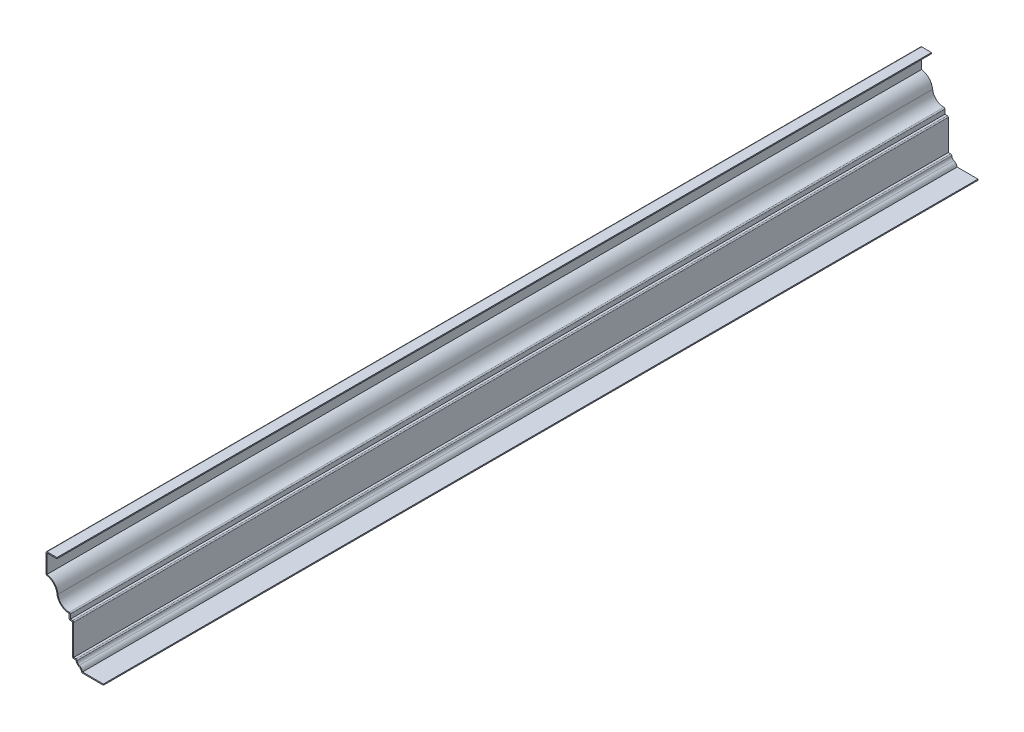
SolidWorks part; units mm, degrees
ref_plane "Front Plane" through (0, 0, 0) normal (0, 0, 1) x (1, 0, 0)
ref_plane "Top Plane" through (0, 0, 0) normal (0, 1, 0) x (1, 0, 0)
ref_plane "Right Plane" through (0, 0, 0) normal (1, 0, 0) x (0, 0, -1)
sketch "Sketch1" plane through (0, 0, 0) normal (0, 0, 1) x (1, 0, 0)
  line L0 (0, 0) -> (-25.4, 0)
  line L1 (-31.75, 9.525) -> (-35.7188, 9.525)
  line L2 (-35.7188, 9.525) -> (-35.7187, 46.0375)
  line L3 (-35.7187, 46.0375) -> (-39.6875, 46.0375)
  line L4 (-39.6875, 46.0375) -> (-39.6875, 52.3875)
  line L5 (-66.675, 77.7875) -> (-66.675, 101.6)
  line L6 (-66.675, 101.6) -> (-53.975, 101.6)
  arc A0 (-25.4, 0) -> (-28.575, 4.7625) centre (-30.5594, 0) ccw
  arc A1 (-28.575, 4.7625) -> (-31.75, 9.525) centre (-26.5906, 9.525) cw
  arc A2 (-39.6875, 52.3875) -> (-53.975, 65.1314) centre (-39.6875, 66.7685) cw
  arc A3 (-53.975, 65.1314) -> (-66.675, 77.7875) centre (-68.2625, 63.4944) ccw
  point P15 (-18.3, 5.8796)
  point P18 (-28.9169, 5.2754)
  point P19 (-53.975, 65.1313)
  point P20 (0, 0)
  dimension "D1" = 101.6
  dimension "D2" = 66.675
  dimension "D3" = 12.7
  dimension "D4" = 23.8125
  dimension "D5" = 6.35
  dimension "D6" = 25.4
  dimension "D7" = 3.9688
  dimension "D8" = 26.9875
  dimension "D9" = 36.5125
  dimension "D10" = 3.9688
  dimension "D11" = 6.35
  dimension "D12" = 9.525
  dimension "D13" = 25.4
extrude "Extrude-Thin1" add sketch "Sketch1" against normal blind 1016 thin
fillet "Fillet1" radius 1.27 8 edges at (-25.4, 0, -508) (-30.2668, 10.795, -508) (-35.7188, 9.525, -508) (-34.4487, 47.3075, -508) (-39.6875, 46.0375, -508) (-38.4175, 53.7192, -508) (-66.675, 77.7875, -508) (-66.675, 101.6, -508)
